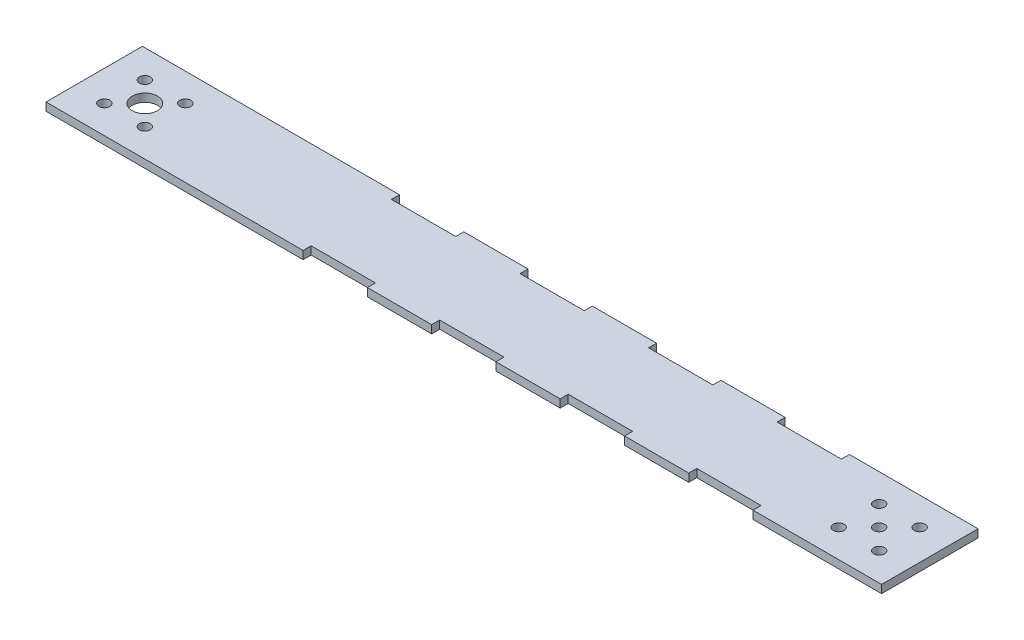
SolidWorks part; units mm, degrees
ref_plane "Front Plane" through (0, 0, 0) normal (0, 0, 1) x (1, 0, 0)
ref_plane "Top Plane" through (0, 0, 0) normal (0, 1, 0) x (1, 0, 0)
ref_plane "Right Plane" through (0, 0, 0) normal (1, 0, 0) x (0, 0, -1)
sketch "Sketch1" plane through (0, 0, 0) normal (0, 1, 0) x (1, 0, 0)
  line L0 (56.2, 15.875) -> (81.6, 15.875) construction
  line L1 (-20, -19.05) -> (310.2, -19.05)
  line L2 (-20, -19.05) -> (-20, 19.05)
  line L3 (-20, 19.05) -> (310.2, 19.05)
  line L4 (310.2, -19.05) -> (310.2, 19.05)
  line L5 (-8, -8) -> (8, -8) construction
  line L6 (-8, -8) -> (-8, 8) construction
  line L7 (-8, 8) -> (8, 8) construction
  line L8 (8, -8) -> (8, 8) construction
  line L9 (-8, -8) -> (8, 8) construction
  line L10 (-8, 8) -> (8, -8) construction
  line L11 (282.2, -8) -> (298.2, -8) construction
  line L12 (282.2, -8) -> (282.2, 8) construction
  line L13 (282.2, 8) -> (298.2, 8) construction
  line L14 (298.2, -8) -> (298.2, 8) construction
  line L15 (282.2, -8) -> (298.2, 8) construction
  line L16 (282.2, 8) -> (298.2, -8) construction
  line L17 (132.4, 19.05) -> (157.8, 19.05)
  line L18 (132.4, 19.05) -> (132.4, 15.875)
  line L19 (132.4, 15.875) -> (157.8, 15.875)
  line L20 (157.8, 19.05) -> (157.8, 15.875)
  line L21 (183.2, 19.05) -> (208.6, 19.05)
  line L22 (183.2, 19.05) -> (183.2, 15.875)
  line L23 (183.2, 15.875) -> (208.6, 15.875)
  line L24 (208.6, 19.05) -> (208.6, 15.875)
  line L25 (81.6, 19.05) -> (107, 19.05)
  line L26 (81.6, 19.05) -> (81.6, 15.875)
  line L27 (81.6, 15.875) -> (107, 15.875)
  line L28 (107, 19.05) -> (107, 15.875)
  line L29 (30.8, 19.05) -> (56.2, 19.05)
  line L30 (30.8, 19.05) -> (30.8, 15.875)
  line L31 (30.8, 15.875) -> (56.2, 15.875)
  line L32 (56.2, 19.05) -> (56.2, 15.875)
  line L33 (30.8, -19.05) -> (56.2, -19.05)
  line L34 (30.8, -19.05) -> (30.8, -15.875)
  line L35 (30.8, -15.875) -> (56.2, -15.875)
  line L36 (56.2, -19.05) -> (56.2, -15.875)
  line L37 (81.6, -19.05) -> (107, -19.05)
  line L38 (81.6, -19.05) -> (81.6, -15.875)
  line L39 (81.6, -15.875) -> (107, -15.875)
  line L40 (107, -19.05) -> (107, -15.875)
  line L41 (132.4, -19.05) -> (157.8, -19.05)
  line L42 (132.4, -19.05) -> (132.4, -15.875)
  line L43 (132.4, -15.875) -> (157.8, -15.875)
  line L44 (157.8, -19.05) -> (157.8, -15.875)
  line L45 (183.2, -19.05) -> (208.6, -19.05)
  line L46 (183.2, -19.05) -> (183.2, -15.875)
  line L47 (183.2, -15.875) -> (208.6, -15.875)
  line L48 (208.6, -19.05) -> (208.6, -15.875)
  line L49 (234, -19.05) -> (259.4, -19.05)
  line L50 (234, -19.05) -> (234, -15.875)
  line L51 (234, -15.875) -> (259.4, -15.875)
  line L52 (259.4, -19.05) -> (259.4, -15.875)
  line L53 (234, 19.05) -> (259.4, 19.05)
  line L54 (234, 19.05) -> (234, 15.875)
  line L55 (234, 15.875) -> (259.4, 15.875)
  line L56 (259.4, 19.05) -> (259.4, 15.875)
  line L57 (107, 15.875) -> (132.4, 15.875) construction
  line L58 (157.8, 15.875) -> (183.2, 15.875) construction
  line L59 (56.2, -15.875) -> (81.6, -15.875) construction
  line L60 (107, -15.875) -> (132.4, -15.875) construction
  line L61 (157.8, -15.875) -> (183.2, -15.875) construction
  line L62 (208.6, -15.875) -> (234, -15.875) construction
  line L63 (208.6, 15.875) -> (234, 15.875) construction
  circle A0 centre (0, 0) radius 5
  circle A1 centre (-8, 8) radius 2.15
  circle A2 centre (8, 8) radius 2.15
  circle A3 centre (8, -8) radius 2.15
  circle A4 centre (-8, -8) radius 2.15
  circle A5 centre (282.2, 8) radius 2.15
  circle A6 centre (298.2, 8) radius 2.15
  circle A7 centre (298.2, -8) radius 2.15
  circle A8 centre (282.2, -8) radius 2.15
  circle A9 centre (290.2, 0) radius 2.15
  point P17 (-20, 0)
  point P18 (290.2, 0)
  point P26 (310.2, 0)
  point P30 (145.1, 19.05)
  point P68 (145.1, 15.875)
  point P70 (145.1, -15.875)
  point P71 (145.1, -19.05)
  dimension "D1" = 10
  dimension "D2" = 4.3
  dimension "D7" = 4.3
  dimension "D3" = 16
  dimension "D4" = 38.1
  dimension "D5" = 20
  dimension "D6" = 330.2
  dimension "D8" = 16
  dimension "D9" = 20
  dimension "D10" = 25.4
  dimension "D11" = 3.175
extrude "Boss-Extrude1" add sketch "Sketch1" along normal mid plane 3.175 contours L3 L56 L55 L54 L24 L23 L22 L20 L19 L18 L28 L27 L26 L32 L31 L30 L2 L1 L34 L35 L36 L38 L39 L40 L42 L43 L44 L46 L47 L48 L50 L51 L52 L4 A9 A8 A7 | L32 L3 L30 L31 | L1 L36 L35 L34
